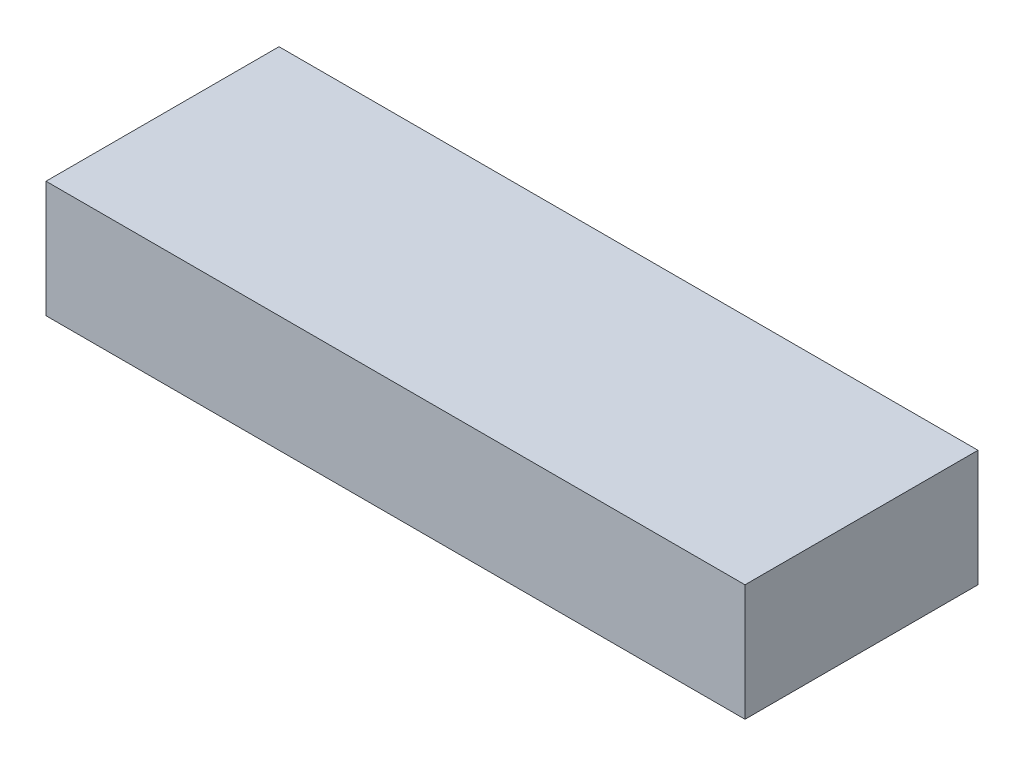
SolidWorks part; units mm, degrees
material "Polyurethane Foam Flexible"
ref_plane "Front Plane" through (0, 0, 0) normal (0, 0, 1) x (1, 0, 0)
ref_plane "Top Plane" through (0, 0, 0) normal (0, 1, 0) x (1, 0, 0)
ref_plane "Right Plane" through (0, 0, 0) normal (1, 0, 0) x (0, 0, -1)
sketch "Sketch1" plane through (0, 0, 0) normal (0, 1, 0) x (1, 0, 0)
  line L0 (0, 25.4) -> (0, -25.4) construction
  line L1 (-76.2, 25.4) -> (76.2, 25.4)
  line L2 (-76.2, 25.4) -> (-76.2, -25.4)
  line L3 (-76.2, -25.4) -> (76.2, -25.4)
  line L4 (76.2, 25.4) -> (76.2, -25.4)
  dimension "D1" = 152.4
  dimension "D2" = 50.8
extrude "Boss-Extrude1" add sketch "Sketch1" along normal blind 25.4
